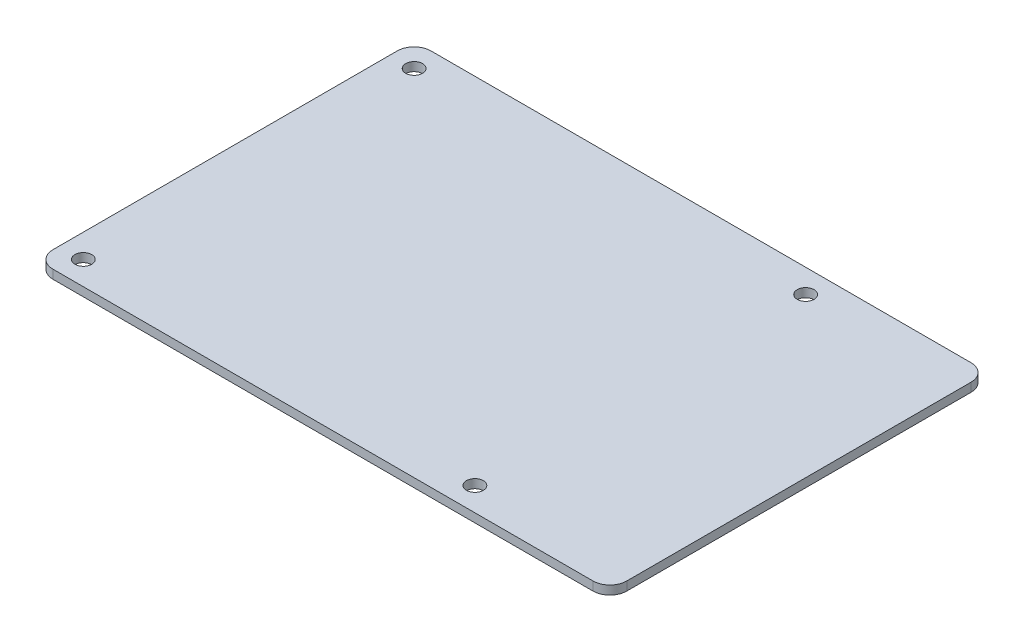
SolidWorks part; units mm, degrees
material "A-Fibra di vetro"
ref_plane "Piano frontale" through (0, 0, 0) normal (0, 0, 1) x (1, 0, 0)
ref_plane "Piano superiore" through (0, 0, 0) normal (0, 1, 0) x (1, 0, 0)
ref_plane "Piano destro" through (0, 0, 0) normal (1, 0, 0) x (0, 0, -1)
sketch "Schizzo1" plane through (0, 0, 0) normal (0, 1, 0) x (1, 0, 0)
  line L0 (42.5, -25.5) -> (42.5, 25.5)
  line L1 (40, 28) -> (-40, 28)
  line L2 (-42.5, 25.5) -> (-42.5, -25.5)
  line L3 (-40, -28) -> (40, -28)
  line L4 (-39, -24.5) -> (19, -24.5) construction
  line L5 (19, -24.5) -> (19, 24.5) construction
  line L6 (19, 24.5) -> (-39, 24.5) construction
  line L7 (-39, 24.5) -> (-39, -24.5) construction
  line L8 (0, 0) -> (19, 0) construction
  line L9 (-41.7678, -27.2678) -> (0, 0) construction
  line L10 (41.7678, -27.2678) -> (0, 0) construction
  line L11 (0, 0) -> (-41.7678, 27.2678) construction
  line L12 (0, 0) -> (41.7678, 27.2678) construction
  line L13 (-41.7678, -27.2678) -> (-39, -24.5) construction
  line L14 (-41.7678, 27.2678) -> (-39, 24.5) construction
  arc A0 (42.5, 25.5) -> (40, 28) centre (40, 25.5) ccw
  arc A1 (-40, 28) -> (-42.5, 25.5) centre (-40, 25.5) ccw
  arc A2 (-42.5, -25.5) -> (-40, -28) centre (-40, -25.5) ccw
  arc A3 (40, -28) -> (42.5, -25.5) centre (40, -25.5) ccw
  circle A4 centre (19, 24.5) radius 1.25
  circle A5 centre (-39, 24.5) radius 1.25
  circle A6 centre (-39, -24.5) radius 1.25
  circle A7 centre (19, -24.5) radius 1.25
  dimension "D3" = 2.5
  dimension "D4" = 2.5
  dimension "D7" = 2.25
  dimension "D10" = 49
  dimension "D1" = 56
  dimension "D2" = 85
  dimension "D5" = 45
  dimension "D6" = 58
  dimension "D8" = 45
extrude "Estrusione-Estrusione1" add sketch "Schizzo1" against normal blind 1.3
